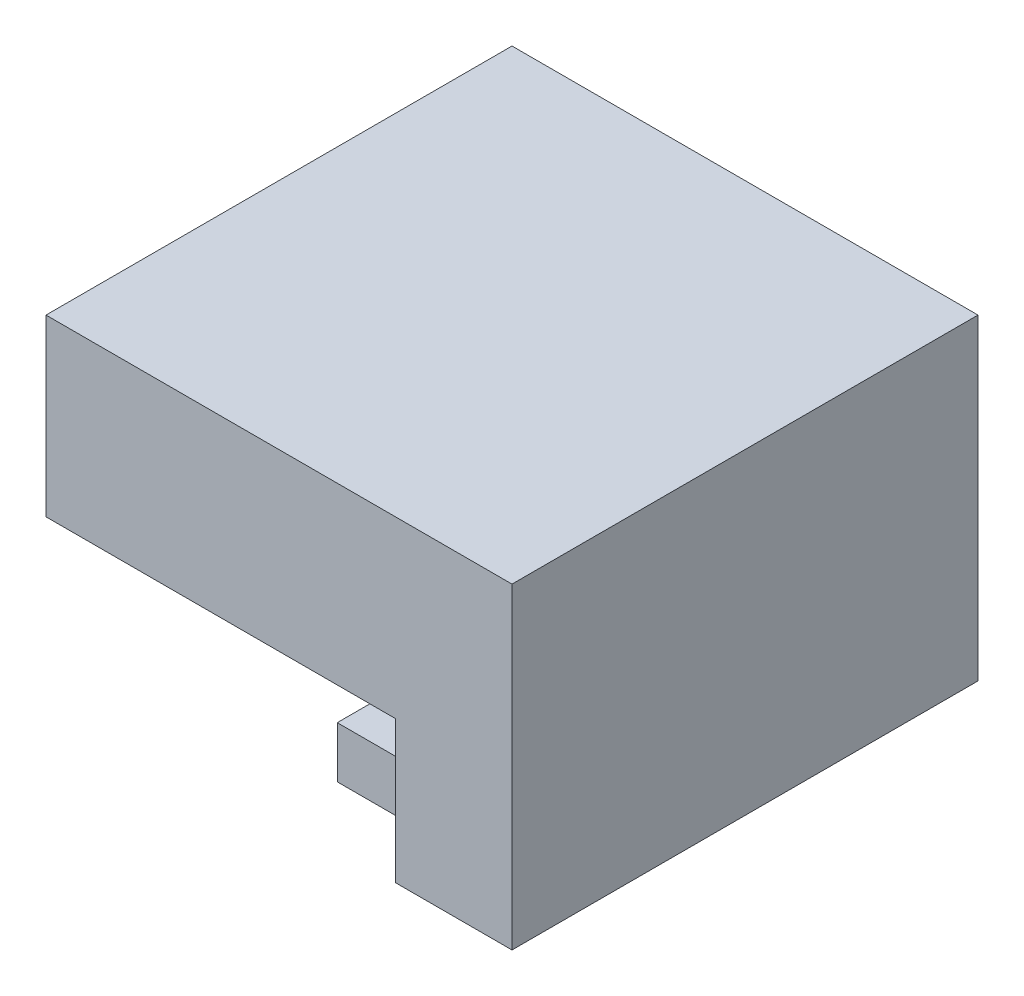
SolidWorks part; units mm, degrees
ref_plane "Front Plane" through (0, 0, 0) normal (0, 0, 1) x (1, 0, 0)
ref_plane "Top Plane" through (0, 0, 0) normal (0, 1, 0) x (1, 0, 0)
ref_plane "Right Plane" through (0, 0, 0) normal (1, 0, 0) x (0, 0, -1)
sketch "Sketch1" plane through (0, 0, 0) normal (1, 0, 0) x (0, 0, -1)
  line L1 (12.7, 4.7625) -> (-12.7, 4.7625)
  line L2 (12.7, 4.7625) -> (12.7, -4.7625)
  line L3 (12.7, -4.7625) -> (-12.7, -4.7625)
  line L4 (-12.7, 4.7625) -> (-12.7, -4.7625)
  line L5 (12.7, 4.7625) -> (-12.7, -4.7625) construction
  line L6 (12.7, -4.7625) -> (-12.7, 4.7625) construction
  arc A0 (-6.35, -4.7625) -> (6.35, -4.7625) centre (0, -4.7625) cw construction
  point P0 (0, 0)
  dimension "D1" = 6.35
  dimension "D2" = 25.4
  dimension "D3" = 9.525
extrude "Boss-Extrude1" add sketch "Sketch1" along normal blind 25.4
sketch "Sketch2" plane through (0, -4.7625, 0) normal (0, -1, 0) x (1, 0, 0)
  line L0 (25.4, -12.7) -> (0, -12.7) construction
  line L1 (25.4, 12.7) -> (19.05, 12.7)
  line L2 (25.4, 12.7) -> (25.4, -12.7)
  line L3 (25.4, -12.7) -> (19.05, -12.7)
  line L4 (19.05, 12.7) -> (19.05, -12.7)
  dimension "D1" = 6.35
extrude "Boss-Extrude2" add sketch "Sketch2" along normal blind 7.747
sketch "Sketch3" plane through (19.05, 0, 0) normal (-1, 0, 0) x (0, 0, 1)
  line L0 (12.7, -12.5095) -> (-12.7, -12.5095) construction
  line L1 (-9.525, -12.5095) -> (9.525, -12.5095)
  line L2 (-9.525, -12.5095) -> (-9.525, -9.7155)
  line L3 (-9.525, -9.7155) -> (9.525, -9.7155)
  line L4 (9.525, -12.5095) -> (9.525, -9.7155)
  line L5 (0, -12.5095) -> (0, 0) construction
  dimension "D1" = 2.794
  dimension "D2" = 19.05
extrude "Boss-Extrude3" add sketch "Sketch3" along normal blind 6.35
sketch "Sketch4" plane through (0, 0, 0) normal (-1, 0, 0) x (0, 0, 1)
  line L0 (12.7, -4.7625) -> (-12.7, -4.7625) construction
  line L1 (12.7, -4.7625) -> (-12.7, -4.7625) construction
  line L2 (-7.62, -4.7625) -> (7.62, -4.7625)
  arc A0 (-7.62, -4.7625) -> (7.62, -4.7625) centre (0, -4.7625) cw
  dimension "D1" = 7.62
extrude "Cut-Extrude1" cut sketch "Sketch4" against normal blind 6.35
